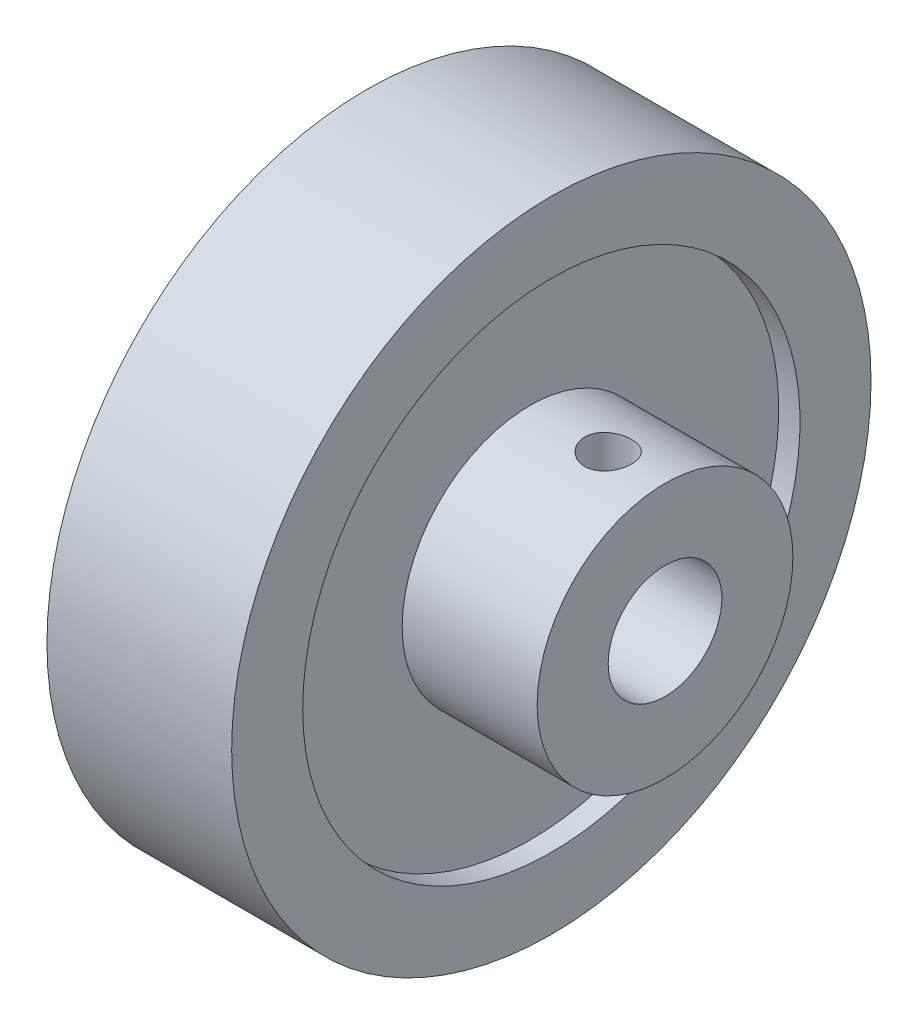
SolidWorks part; units mm, degrees
material "6061 Alloy"
ref_plane "Front Plane" through (0, 0, 0) normal (0, 0, 1) x (1, 0, 0)
ref_plane "Top Plane" through (0, 0, 0) normal (0, 1, 0) x (1, 0, 0)
ref_plane "Right Plane" through (0, 0, 0) normal (1, 0, 0) x (0, 0, -1)
sketch "Sketch1" plane through (0, 0, 0) normal (0, 0, 1) x (1, 0, 0)
  line L0 (0, 0) -> (10, 0) construction
  line L2 (-6.5, 4) -> (6.5, 4)
  line L3 (-6.5, 4) -> (-6.5, 9)
  line L4 (-6.5, 9) -> (6.5, 9)
  line L5 (6.5, 4) -> (6.5, 9)
  line L6 (-5, 9) -> (5, 9)
  line L7 (-5, 9) -> (-5, 17.5)
  line L8 (-5, 17.5) -> (5, 17.5)
  line L9 (5, 9) -> (5, 17.5)
  line L10 (-6.5, 17.5) -> (6.5, 17.5)
  line L11 (-6.5, 17.5) -> (-6.5, 22.5)
  line L12 (-6.5, 22.5) -> (6.5, 22.5)
  line L13 (6.5, 17.5) -> (6.5, 22.5)
  line L18 (14.5, 9) -> (6.5, 9)
  line L19 (14.5, 9) -> (14.5, 4)
  line L20 (14.5, 4) -> (6.5, 4)
  line L21 (6.5, 9) -> (6.5, 4)
  point P15 (0, 22.5)
  point P16 (0, 17.5)
  point P17 (0, 4)
  dimension "D1" = 10
  dimension "D2" = 5
  dimension "D3" = 13
  dimension "D4" = 4
  dimension "D5" = 22.5
  dimension "D6" = 10
  dimension "D7" = 8
revolve "Revolve1" add sketch "Sketch1" angle 360 about L0
ref_plane "Plane1" through (0, 9, 0) normal (0, 1, 0) x (1, 0, 0)
hole_wizard "M4 Tapped Hole1" positions "Sketch2" profile "Sketch3" tap size "M4" standard "ISO"
sketch "Sketch2" plane through (0, 9, 0) normal (0, 1, 0) x (1, 0, 0)
  line L0 (14.5, -9) -> (14.5, 9) construction
  point P0 (10.5, 0)
  dimension "D1" = 4
sketch "Sketch3" plane through (10.5, 9, 0) normal (1, 0, 0) x (0, 0, 1)
  line L0 (0, 0) -> (0, 5)
  line L1 (0, 5) -> (1.65, 5)
  line L2 (1.65, 5) -> (1.65, 0)
  line L5 (1.65, 0) -> (0, 0)
  line L11 (0, -6.35) -> (0, 107.95) construction
  dimension "Thru Tap Drill Dia." = 3.3
  dimension "Thru Tap Drill Depth" = 5
cosmetic thread "Hole Thread1" parameters "D2"=4
